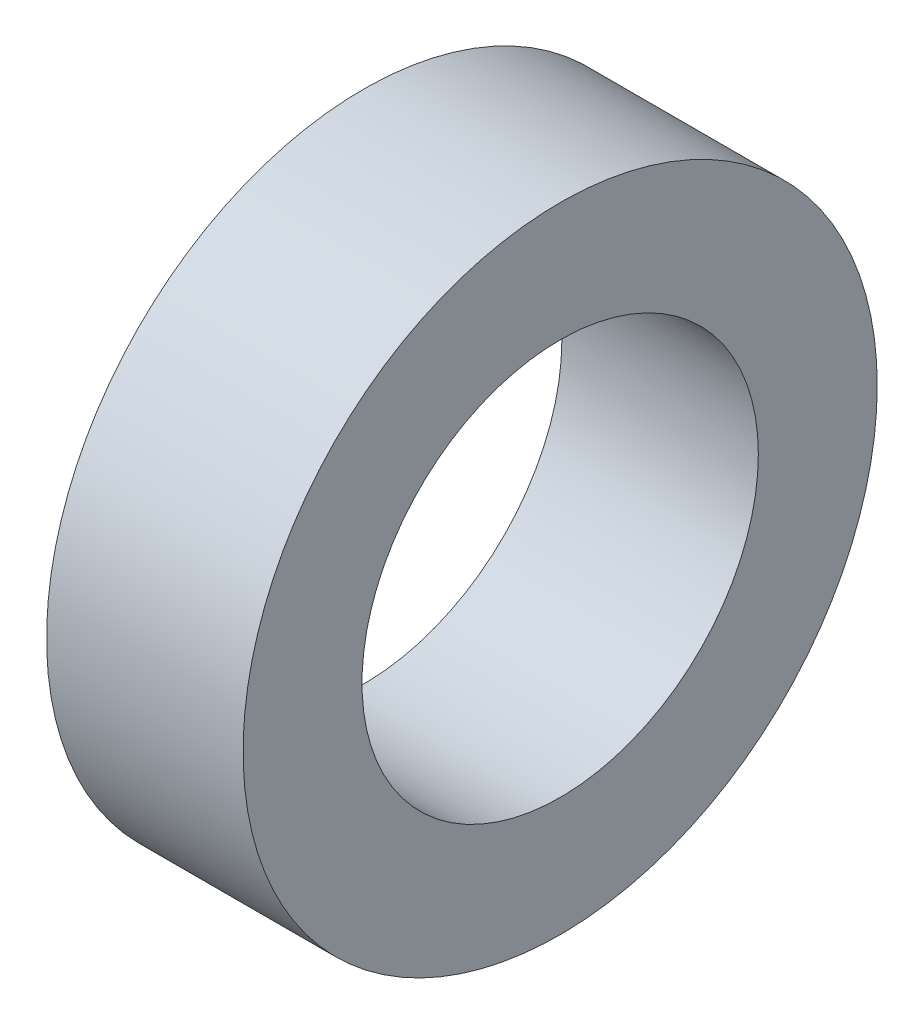
SolidWorks part; units mm, degrees
material "ABS PC"
ref_plane "Front Plane" through (0, 0, 0) normal (0, 0, 1) x (1, 0, 0)
ref_plane "Top Plane" through (0, 0, 0) normal (0, 1, 0) x (1, 0, 0)
ref_plane "Right Plane" through (0, 0, 0) normal (1, 0, 0) x (0, 0, -1)
sketch "Sketch1" plane through (0, 0, 0) normal (1, 0, 0) x (0, 0, -1)
  circle A0 centre (0, 0) radius 6.35
  circle A1 centre (0, 0) radius 10.16
  dimension "D1" = 20.32
  dimension "D2" = 12.7
extrude "Boss-Extrude1" add sketch "Sketch1" along normal blind 6.2967
